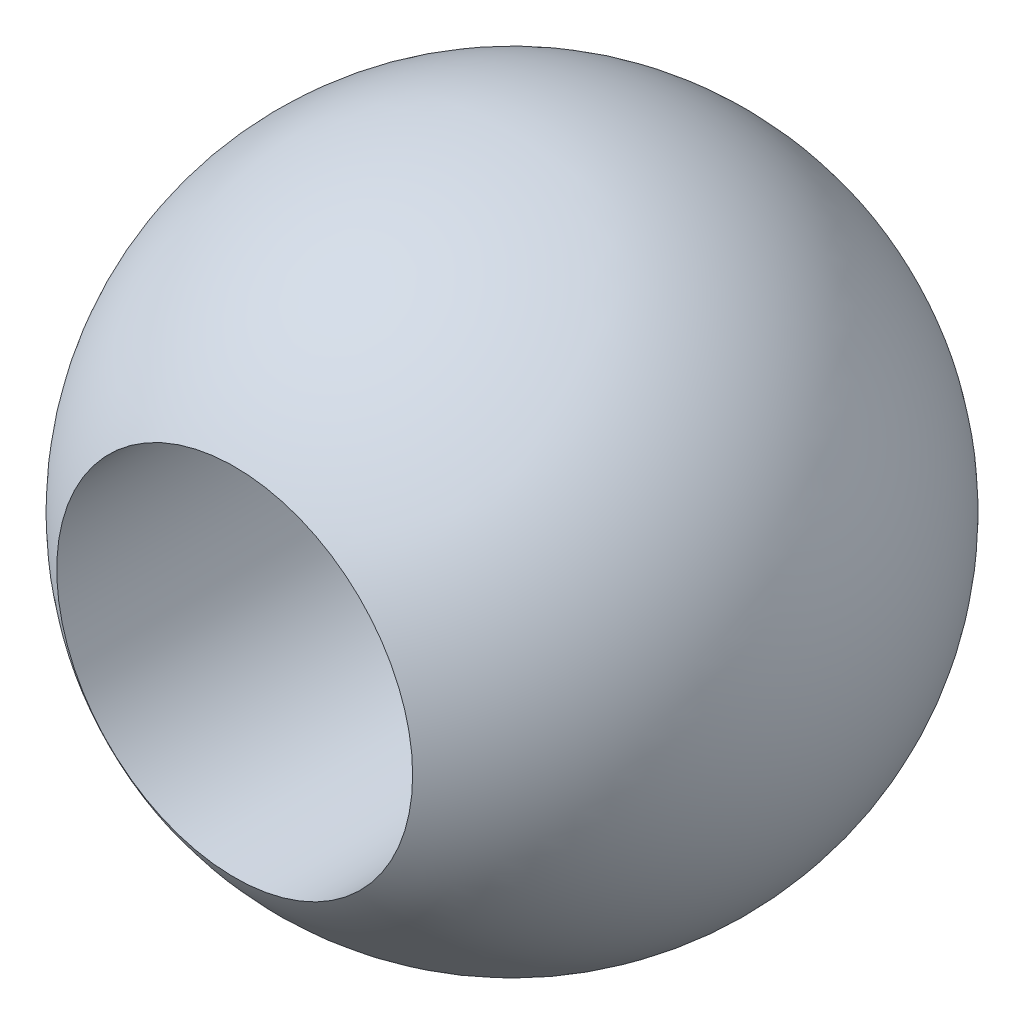
SolidWorks part; units mm, degrees
ref_plane "Front Plane" through (0, 0, 0) normal (0, 0, 1) x (1, 0, 0)
ref_plane "Top Plane" through (0, 0, 0) normal (0, 1, 0) x (1, 0, 0)
ref_plane "Right Plane" through (0, 0, 0) normal (1, 0, 0) x (0, 0, -1)
sketch "Sketch1" plane through (0, 0, 0) normal (0, 1, 0) x (1, 0, 0)
  line L0 (0, 0) -> (3.429, 0)
  line L1 (3.429, 0) -> (3.429, -5.3446)
  line L2 (0, 0) -> (0, 6.35)
  arc A1 (0, 6.35) -> (3.429, -5.3446) centre (0, 0) cw
  dimension "D1" = 3.429
  dimension "D2" = 6.35
revolve "Revolve1" add sketch "Sketch1" angle 360 about L2
